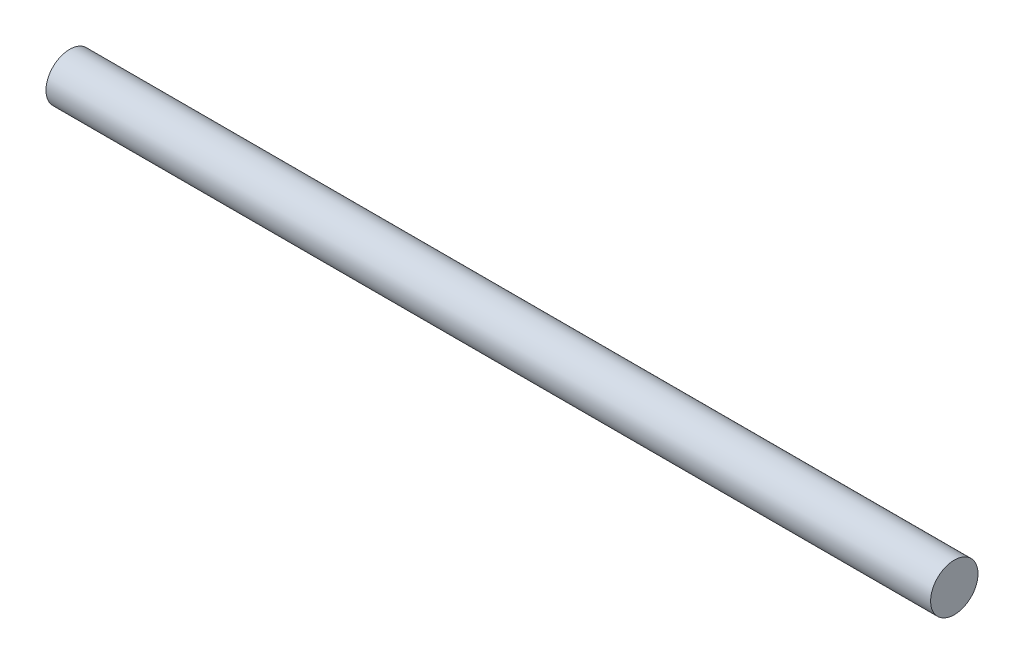
SolidWorks part; units mm, degrees
ref_plane "Front Plane" through (0, 0, 0) normal (0, 0, 1) x (1, 0, 0)
ref_plane "Top Plane" through (0, 0, 0) normal (0, 1, 0) x (1, 0, 0)
ref_plane "Right Plane" through (0, 0, 0) normal (1, 0, 0) x (0, 0, -1)
sketch "Sketch1" plane through (0, 0, 0) normal (1, 0, 0) x (0, 0, -1)
  circle A0 centre (0, 0) radius 15
  dimension "D1" = 30
extrude "Boss-Extrude1" add sketch "Sketch1" along normal blind 560 contours A0
